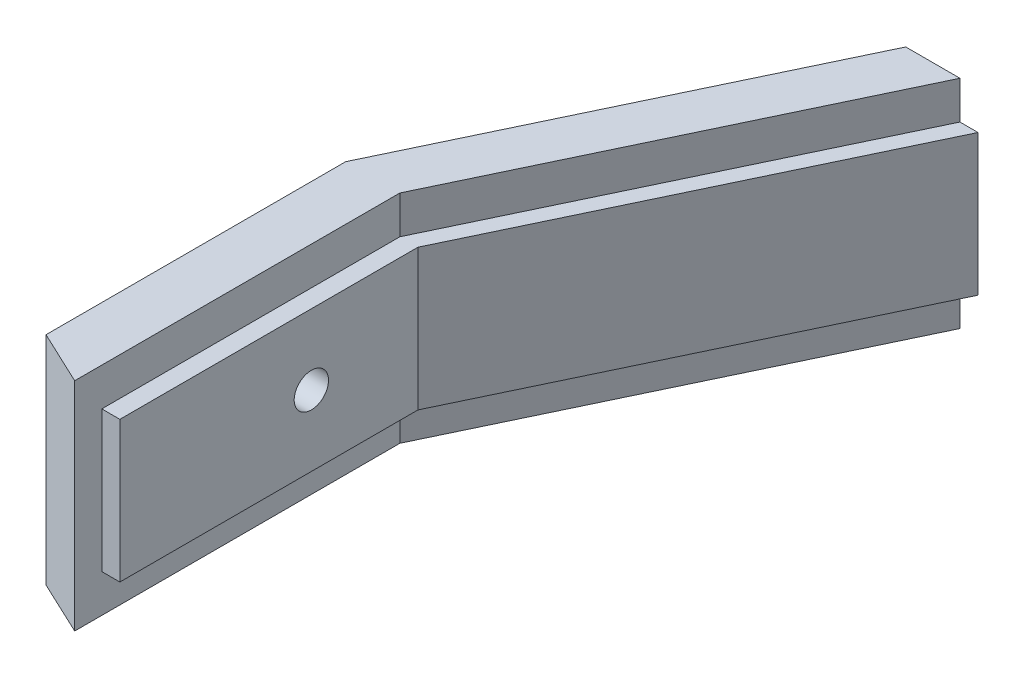
SolidWorks part; units mm, degrees
ref_plane "Front Plane" through (0, 0, 0) normal (0, 0, 1) x (1, 0, 0)
ref_plane "Top Plane" through (0, 0, 0) normal (0, 1, 0) x (1, 0, 0)
ref_plane "Right Plane" through (0, 0, 0) normal (1, 0, 0) x (0, 0, -1)
sketch "Sketch1" plane through (0, 0, 0) normal (1, 0, 0) x (0, 0, -1)
  line L1 (0, 0) -> (-16.5, 0)
  line L2 (0, 0) -> (0, 7.8)
  line L3 (0, 7.8) -> (-16.5, 7.8)
  line L4 (-16.5, 0) -> (-16.5, 7.8)
  dimension "D1" = 16.5
  dimension "D2" = 7.8
extrude "Boss-Extrude1" add sketch "Sketch1" along normal blind 1
sketch "Sketch2" plane through (0, 0, 0) normal (-1, 0, 0) x (0, 0, 1)
  line L0 (16.5, 3.9) -> (0, 3.9) construction
  line L1 (16.5, 7.8) -> (16.5, 0) construction
  line L2 (0, 0) -> (0, 7.8) construction
  line L3 (0, -2.1) -> (0, 9.9)
  line L4 (0, 9.9) -> (18, 9.9)
  line L5 (18, 9.9) -> (18, -2.1)
  line L6 (18, -2.1) -> (0, -2.1)
  point P9 (0, 3.9)
  dimension "D1" = 12
  dimension "D2" = 1.5
extrude "Boss-Extrude2" add sketch "Sketch2" along normal blind 3
sketch "Sketch3" plane through (0, 0, 0) normal (0, 0, -1) x (-1, 0, 0)
  line L0 (0, 7.8) -> (0, 9.9)
  line L1 (0, 9.9) -> (3, 9.9)
  line L2 (3, 9.9) -> (3, -2.1)
  line L3 (3, 9.9) -> (3, -2.1) construction
  line L4 (3, -2.1) -> (0, -2.1)
  line L5 (3, -2.1) -> (0, -2.1) construction
  line L6 (0, -2.1) -> (0, 0)
  line L7 (0, 0) -> (-1, 0)
  line L8 (-1, 0) -> (-1, 7.8)
  line L9 (-1, 7.8) -> (0, 7.8)
ref_plane "Plane1" through (0, 0, -25) normal (0, 0, -1) x (-1, 0, 0)
ref_plane "Plane2" through (0, 0, -21) normal (0, 0, -1) x (-1, 0, 0)
sketch "Sketch4" plane through (0, 0, -21) normal (0, 0, -1) x (-1, 0, 0)
  line L0 (-11, 7.8) -> (-10, 7.8)
  line L1 (-10, 7.8) -> (-10, 9.9)
  line L2 (-10, 9.9) -> (-7, 9.9)
  line L3 (-7, 9.9) -> (-7, -2.1)
  line L4 (-7, -2.1) -> (-10, -2.1)
  line L5 (-10, -2.1) -> (-10, 0)
  line L6 (-10, 0) -> (-11, 0)
  line L7 (-11, 0) -> (-11, 7.8)
  line L8 (3, 9.9) -> (3, -2.1) construction
  dimension "D1" = 1
  dimension "D2" = 3
  dimension "D3" = 10
  dimension "D4" = 3
loft "Loft1" add profiles "Sketch3", "Sketch4"
sketch "Sketch5" plane through (0, 9.9, 0) normal (0, 1, 0) x (1, 0, 0)
  line L0 (0, -18) -> (-3, -18)
  line L1 (-3, -18) -> (-3, -16.5883)
  line L2 (-3, -18) -> (-3, 0) construction
  line L3 (-3, -16.5883) -> (0, -18)
  dimension "D1" = 25.2
extrude "Cut-Extrude1" cut sketch "Sketch5" against normal up to surface (12 mm away) up to face at (0.4167, -2.1, 2.5)
sketch "Sketch6" plane through (1, 0, 0) normal (1, 0, 0) x (0, 0, -1)
  line L0 (-16.5, 3.9) -> (0, 3.9) construction
  line L1 (-16.5, 7.8) -> (-16.5, 0) construction
  line L2 (0, 0) -> (0, 7.8) construction
  line L3 (-16.5, 7.8) -> (-16.5, 0) construction
  circle A0 centre (-5.9, 3.9) radius 0.95
  point P6 (-5.9, 3.9)
  dimension "D2" = 1.9
  dimension "D1" = 10.6
extrude "Cut-Extrude2" cut sketch "Sketch6" against normal up to surface (4 mm away) up to face at (-3, 3.9, 8.2942)
sketch "Sketch8" plane through (-3, 0, 0) normal (-1, 0, 0) x (0, 0, 1)
  circle A0 centre (5.9, 3.9) radius 2.5
  dimension "D1" = 5
extrude "Cut-Extrude3" cut sketch "Sketch8" against normal blind 2.5 contours A0
